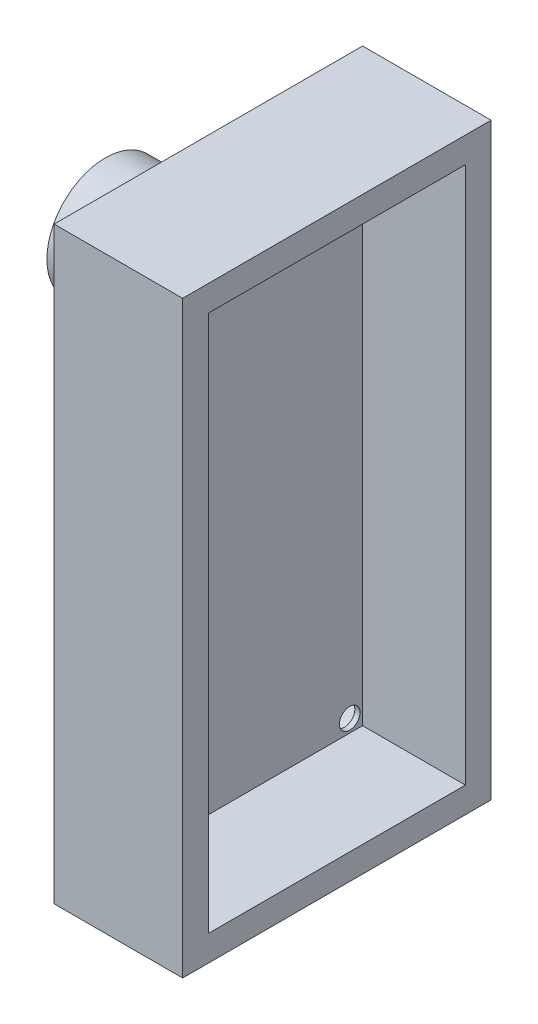
SolidWorks part; units mm, degrees
ref_plane "Alzado" through (0, 0, 0) normal (0, 0, 1) x (1, 0, 0)
ref_plane "Planta" through (0, 0, 0) normal (0, 1, 0) x (1, 0, 0)
ref_plane "Vista lateral" through (0, 0, 0) normal (1, 0, 0) x (0, 0, -1)
sketch "Croquis1" plane through (0, 0, 0) normal (1, 0, 0) x (0, 0, -1)
  line L1 (-11.9876, -12.7099) -> (-23.9876, -12.7099)
  line L2 (-11.9876, -12.7099) -> (-11.9876, -35.6099)
  line L3 (-11.9876, -35.6099) -> (-23.9876, -35.6099)
  line L4 (-23.9876, -12.7099) -> (-23.9876, -35.6099)
  dimension "D1" = 12
  dimension "D2" = 22.9
extrude "Saliente-Extruir1" add sketch "Croquis1" along normal blind 5
shell "Vaciado2" thickness 1
sketch "Croquis2" plane through (0, 0, 0) normal (-1, 0, 0) x (0, 0, 1)
  line L0 (17.9876, -12.7099) -> (17.9876, -17.7544)
  line L1 (11.9876, -12.7099) -> (23.9876, -12.7099) construction
  circle A0 centre (17.9876, -17.7544) radius 2.28
extrude "Saliente-Extruir2" add sketch "Croquis2" along normal blind 4
sketch "Croquis4" plane through (0, 0, 0) normal (-1, 0, 0) x (0, 0, 1)
  line L0 (12.6437, -12.7099) -> (12.6437, -14.2099)
  line L1 (11.9876, -12.7099) -> (23.9876, -12.7099) construction
  line L2 (11.9876, -14.2099) -> (13.4876, -14.2099)
  line L3 (11.9876, -35.6099) -> (11.9876, -12.7099) construction
  line L4 (22.3099, -12.7099) -> (22.3099, -14.2099)
  line L5 (23.9876, -14.2099) -> (22.4876, -14.2099)
  line L6 (23.9876, -12.7099) -> (23.9876, -35.6099) construction
  line L7 (11.9876, -34.028) -> (13.4876, -34.028)
  line L8 (13.4876, -35.6099) -> (13.4876, -34.1099)
  line L9 (23.9876, -35.6099) -> (11.9876, -35.6099) construction
  line L10 (23.9876, -34.1099) -> (22.4876, -34.1099)
  line L11 (22.4876, -35.6099) -> (22.4876, -34.1099)
  circle A0 centre (13.4876, -14.2099) radius 1
  circle A1 centre (22.4876, -14.2099) radius 1
  circle A2 centre (13.4876, -34.1099) radius 1
  circle A3 centre (22.4876, -34.1099) radius 1
extrude "Cortar-Extruir1" cut sketch "Croquis4" against normal blind 0.8
sketch "Croquis5" plane through (0.8, 0, 0) normal (-1, 0, 0) x (0, 0, 1)
  circle A0 centre (13.4876, -14.2099) radius 0.4
  circle A1 centre (22.4876, -14.2099) radius 0.4
  circle A2 centre (13.4876, -34.1099) radius 0.4
  circle A3 centre (22.4876, -34.1099) radius 0.4
extrude "Cortar-Extruir2" cut sketch "Croquis5" against normal blind 0.8
